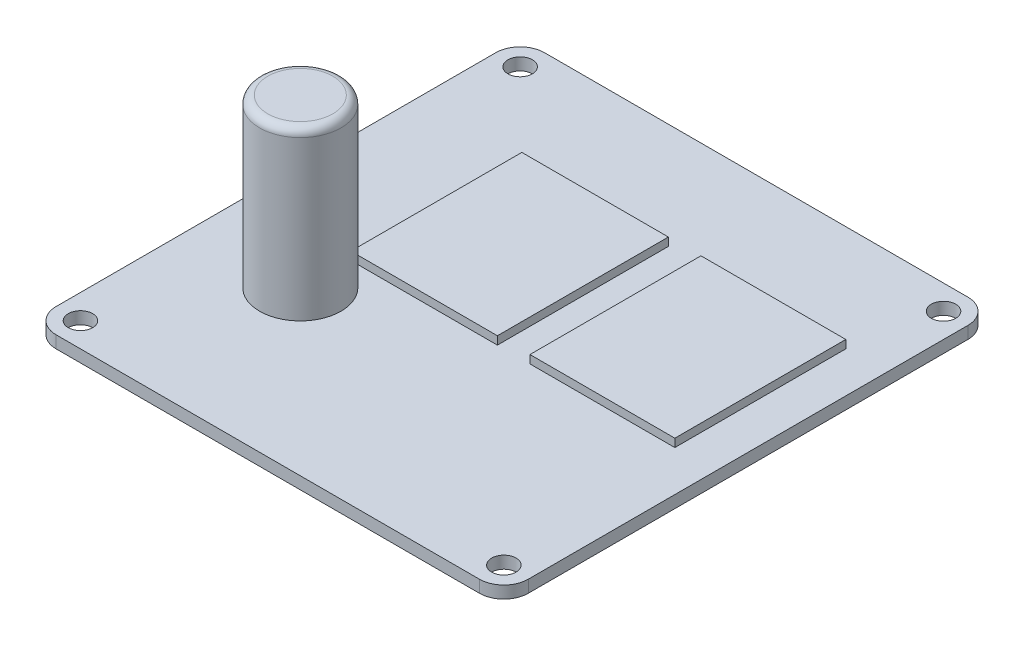
SolidWorks part; units mm, degrees
ref_plane "Front Plane" through (0, 0, 0) normal (0, 0, 1) x (1, 0, 0)
ref_plane "Top Plane" through (0, 0, 0) normal (0, 1, 0) x (1, 0, 0)
ref_plane "Right Plane" through (0, 0, 0) normal (1, 0, 0) x (0, 0, -1)
sketch "Sketch1" plane through (0, 0, 0) normal (0, 1, 0) x (1, 0, 0)
  line L1 (-26, 30) -> (26, 30)
  line L2 (-29, 27) -> (-29, -27)
  line L3 (-26, -30) -> (26, -30)
  line L4 (29, 27) -> (29, -27)
  line L5 (-29, 30) -> (29, -30) construction
  line L6 (-29, -30) -> (29, 30) construction
  line L8 (0, 0) -> (0, 33.9107) construction
  line L9 (0, 33.9107) -> (0, -29.8791) construction
  line L10 (0, -29.8791) -> (0, -35.7325) construction
  line L11 (0, 0) -> (37.2478, 0) construction
  line L12 (37.2478, 0) -> (-35.8597, 0) construction
  line L13 (7.7252, -11.8113) -> (7.7252, 20.7306) construction
  line L14 (-13, -17) -> (13, -17)
  line L15 (-13, -17) -> (-13, -26)
  line L16 (-13, -26) -> (13, -26)
  line L17 (13, -17) -> (13, -26)
  line L18 (24, 16) -> (9, 16)
  line L19 (24, 16) -> (24, -10)
  line L20 (24, -10) -> (9, -10)
  line L21 (9, 16) -> (9, -10)
  line L22 (-8.5496, -10) -> (6.4504, -10)
  line L23 (-8.5496, 16) -> (-8.5496, -10)
  line L24 (-8.5496, 16) -> (6.4504, 16)
  line L25 (6.4504, 16) -> (6.4504, -10)
  circle A0 centre (-26, 27) radius 1.5
  circle A1 centre (-26, -27) radius 1.5
  circle A2 centre (26, -27) radius 1.5
  circle A3 centre (26, 27) radius 1.5
  arc A4 (-26, 30) -> (-29, 27) centre (-26, 27) ccw
  arc A5 (26, 30) -> (29, 27) centre (26, 27) cw
  arc A6 (-29, -27) -> (-26, -30) centre (-26, -27) ccw
  arc A7 (26, -30) -> (29, -27) centre (26, -27) ccw
  circle A8 centre (-19, -8) radius 6
  point P1 (0, 0)
  dimension "D3" = 3
  dimension "D4" = 3
  dimension "D5" = 3
  dimension "D6" = 3
  dimension "D7" = 3
  dimension "D8" = 3
  dimension "D9" = 3
  dimension "D16" = 12
  dimension "D1" = 60
  dimension "D2" = 58
  dimension "D10" = 4
  dimension "D11" = 16
  dimension "D12" = 16
  dimension "D13" = 9
  dimension "D14" = 22
  dimension "D15" = 10
  dimension "D17" = 5
  dimension "D18" = 20
  dimension "D19" = 14
  dimension "D20" = 15
extrude "Boss-Extrude2" add sketch "Sketch1" against normal blind 1.5 contours L2 A6 L3 A7 L4 A5 L1 A4
sketch "Sketch3" plane through (0, 0, 0) normal (0, 1, 0) x (1, 0, 0)
  line L0 (29, 27) -> (29, -27) construction
  line L5 (6.2073, 17) -> (24, 17)
  line L6 (6.2073, 17) -> (6.2073, -4)
  line L7 (6.2073, -4) -> (24, -4)
  line L8 (24, 17) -> (24, -4)
  line L9 (-15.7927, 17) -> (2.2073, 17)
  line L10 (-15.7927, 17) -> (-15.7927, -4)
  line L11 (-15.7927, -4) -> (2.2073, -4)
  line L12 (2.2073, 17) -> (2.2073, -4)
  line L15 (-26, 30) -> (26, 30) construction
  dimension "D7" = 18
  dimension "D8" = 17.7927
  dimension "D9" = 21
  dimension "D10" = 5
  dimension "D11" = 4
  dimension "D12" = 13
  dimension "D13" = 21
  dimension "D14" = 13
extrude "Boss-Extrude4" add sketch "Sketch3" along normal blind 1
sketch "Sketch5" plane through (0, 0, 0) normal (0, 1, 0) x (1, 0, 0)
  line L0 (-29, 27) -> (-29, -27) construction
  line L1 (-26, -30) -> (26, -30) construction
  circle A0 centre (-16, -10) radius 5
  dimension "D1" = 13
  dimension "D2" = 10
  dimension "D3" = 20
extrude "Boss-Extrude6" add sketch "Sketch5" along normal blind 20.5
fillet "Fillet4" radius 1 1 edges at (-16, 20.5, 15)
sketch "Sketch6" plane through (0, 0, 0) normal (0, 1, 0) x (1, 0, 0)
  line L0 (-29, 27) -> (-29, -27) construction
  line L1 (-26, 30) -> (26, 30) construction
  line L2 (29, 0) -> (-29, 0) construction
  line L3 (29, 27) -> (29, -27) construction
  line L4 (0, 30) -> (0, -30) construction
  line L5 (-26, -30) -> (26, -30) construction
  circle A0 centre (-26, 27) radius 1.5
  circle A1 centre (26, 27) radius 1.5
  circle A2 centre (-26, -27) radius 1.5
  circle A3 centre (26, -27) radius 1.5
  dimension "D1" = 3
  dimension "D3" = 3
  dimension "D2" = 3
extrude "Cut-Extrude1" cut sketch "Sketch6" against normal up to next
